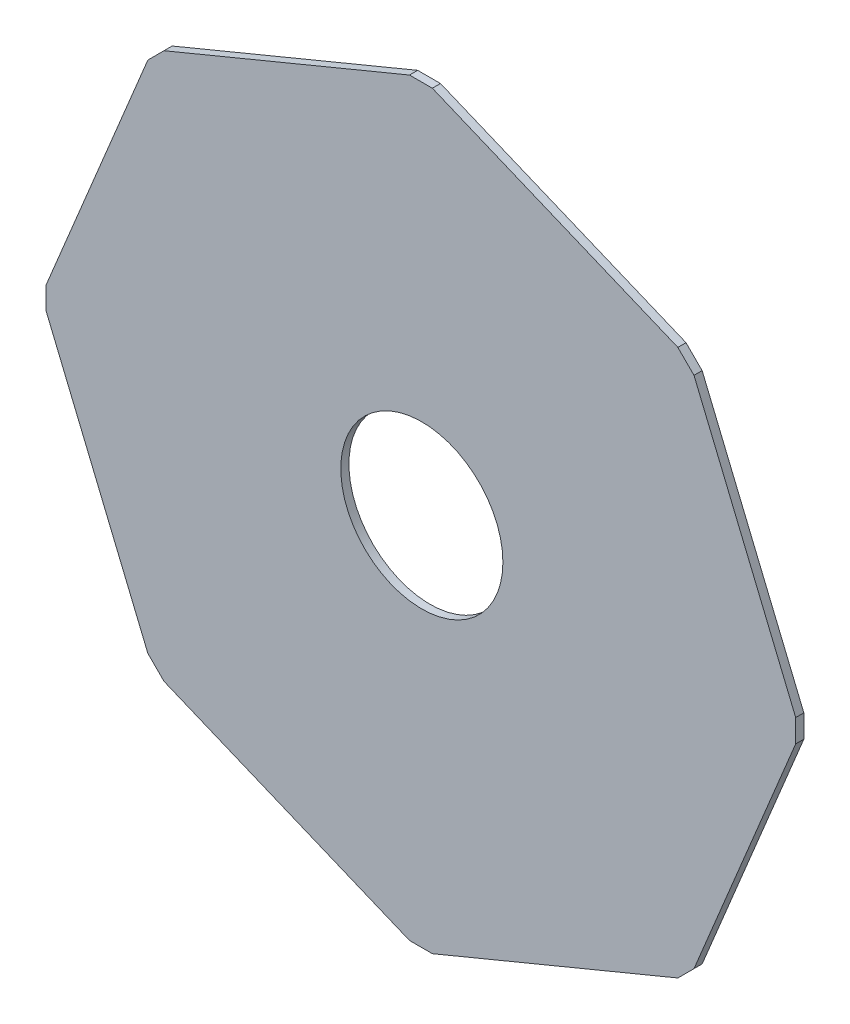
SolidWorks part; units mm, degrees
ref_plane "Front Plane" through (0, 0, 0) normal (0, 0, 1) x (1, 0, 0)
ref_plane "Top Plane" through (0, 0, 0) normal (0, 1, 0) x (1, 0, 0)
ref_plane "Right Plane" through (0, 0, 0) normal (1, 0, 0) x (0, 0, -1)
sketch "Sketch1" plane through (0, 0, 0) normal (0, 0, 1) x (1, 0, 0)
  line L0 (-230.5579, -6.721) -> (-168.1422, -157.4058)
  line L1 (-168.1422, -157.4058) -> (-158.2428, -167.3053)
  line L2 (-158.2428, -167.3053) -> (-7.5579, -229.721)
  line L3 (-7.5579, -229.721) -> (6.4421, -229.721)
  line L4 (6.4421, -229.721) -> (157.1269, -167.3053)
  line L5 (157.1269, -167.3053) -> (167.0264, -157.4058)
  line L6 (167.0264, -157.4058) -> (229.4421, -6.721)
  line L7 (229.4421, -6.721) -> (229.4421, 7.279)
  line L8 (229.4421, 7.279) -> (167.0264, 157.9638)
  line L9 (167.0264, 157.9638) -> (157.1269, 167.8633)
  line L10 (157.1269, 167.8633) -> (6.4421, 230.279)
  line L11 (6.4421, 230.279) -> (-7.5579, 230.279)
  line L12 (-7.5579, 230.279) -> (-158.2428, 167.8633)
  line L13 (-158.2428, 167.8633) -> (-168.1422, 157.9638)
  line L14 (-168.1422, 157.9638) -> (-230.5579, 7.279)
  line L15 (-230.5579, 7.279) -> (-230.5579, -6.721)
  circle A0 centre (0, 0) radius 49.75
  dimension "D3" = 99.5
  dimension "D1" = 150.6848
  dimension "D2" = 163.1001
extrude "Boss-Extrude1" add sketch "Sketch1" along normal blind 5
